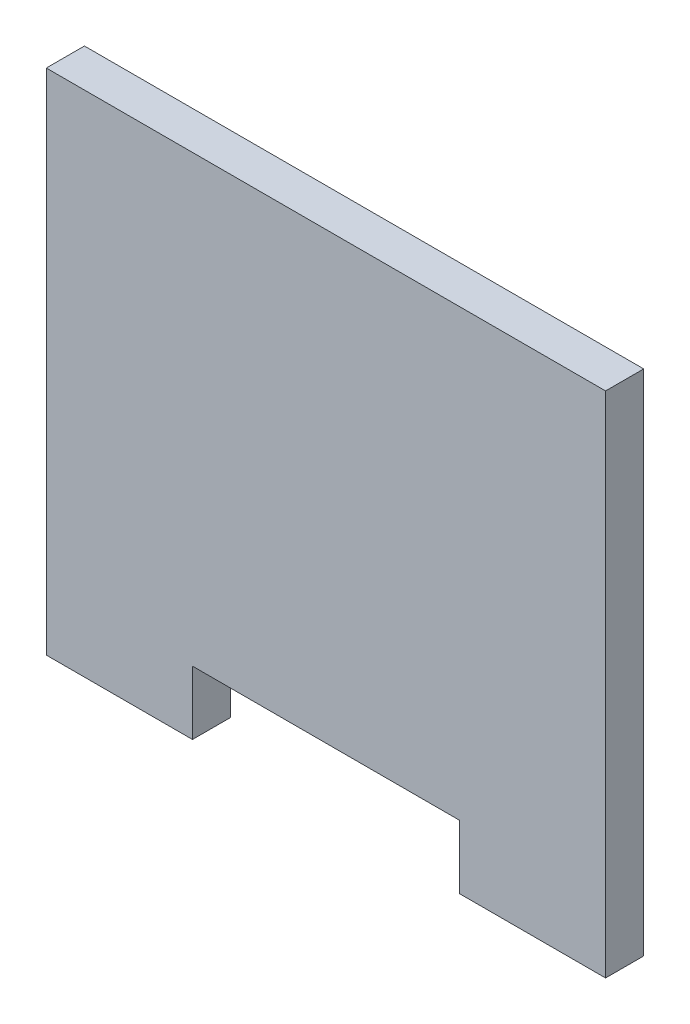
SolidWorks part; units mm, degrees
ref_plane "前视" through (0, 0, 0) normal (0, 0, 1) x (1, 0, 0)
ref_plane "上视" through (0, 0, 0) normal (0, 1, 0) x (1, 0, 0)
ref_plane "右视" through (0, 0, 0) normal (1, 0, 0) x (0, 0, -1)
sketch "草图1" plane through (0, 0, 0) normal (0, 0, 1) x (1, 0, 0)
  line L1 (-22.6948, 30.5659) -> (21.3052, 30.5659)
  line L2 (-22.6948, 30.5659) -> (-22.6948, -9.4341)
  line L3 (-22.6948, -9.4341) -> (-11.1948, -9.4341)
  line L4 (21.3052, 30.5659) -> (21.3052, -9.4341)
  line L5 (9.8052, -4.4341) -> (9.8052, -9.4341)
  line L6 (-0.6948, 33.3651) -> (-0.6948, -21.3108) construction
  line L7 (-11.1948, -4.4341) -> (-11.1948, -9.4341)
  line L8 (9.8052, -9.4341) -> (21.3052, -9.4341)
  line L9 (-11.1948, -4.4341) -> (9.8052, -4.4341)
  dimension "D1" = 11.5
  dimension "D2" = 40
  dimension "D3" = 21
  dimension "D4" = 5
  dimension "D5" = 11.5
extrude "凸台-拉伸1" add sketch "草图1" along normal blind 3
